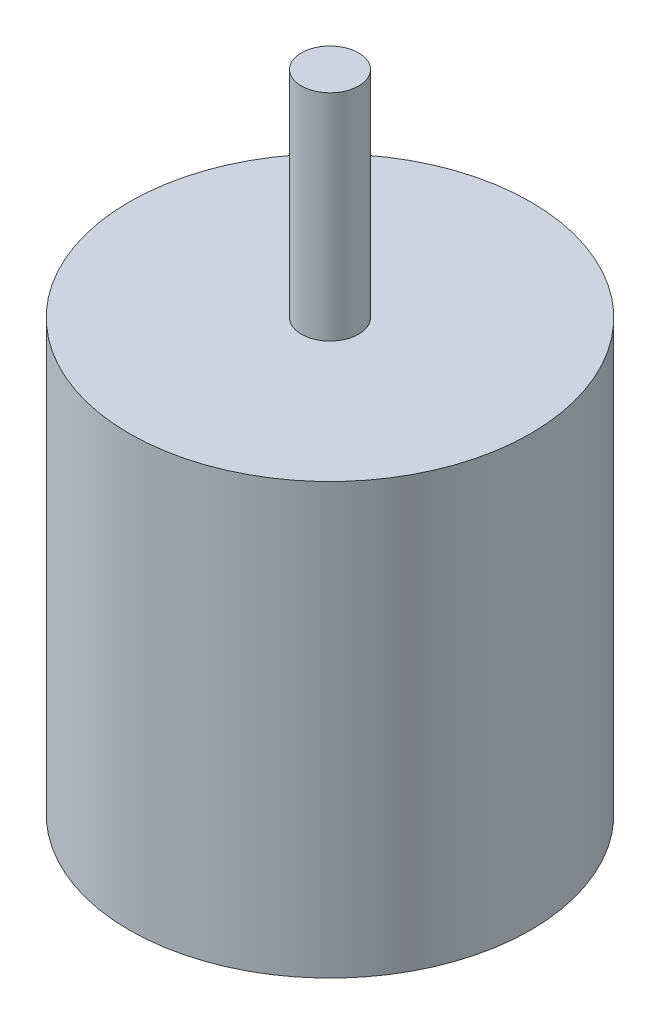
SolidWorks part; units mm, degrees
material "6061-T6 (SS)"
ref_plane "Front Plane" through (0, 0, 0) normal (0, 0, 1) x (1, 0, 0)
ref_plane "Top Plane" through (0, 0, 0) normal (0, 1, 0) x (1, 0, 0)
ref_plane "Right Plane" through (0, 0, 0) normal (1, 0, 0) x (0, 0, -1)
sketch "Sketch1" plane through (0, 0, 0) normal (0, 1, 0) x (1, 0, 0)
  circle A0 centre (0, 0) radius 14
  dimension "D1" = 28
extrude "Boss-Extrude1" add sketch "Sketch1" along normal blind 30
sketch "Sketch2" plane through (0, 30, 0) normal (0, 1, 0) x (1, 0, 0)
  circle A0 centre (0, 0) radius 2
  dimension "D1" = 4
extrude "Boss-Extrude2" add sketch "Sketch2" along normal blind 15
